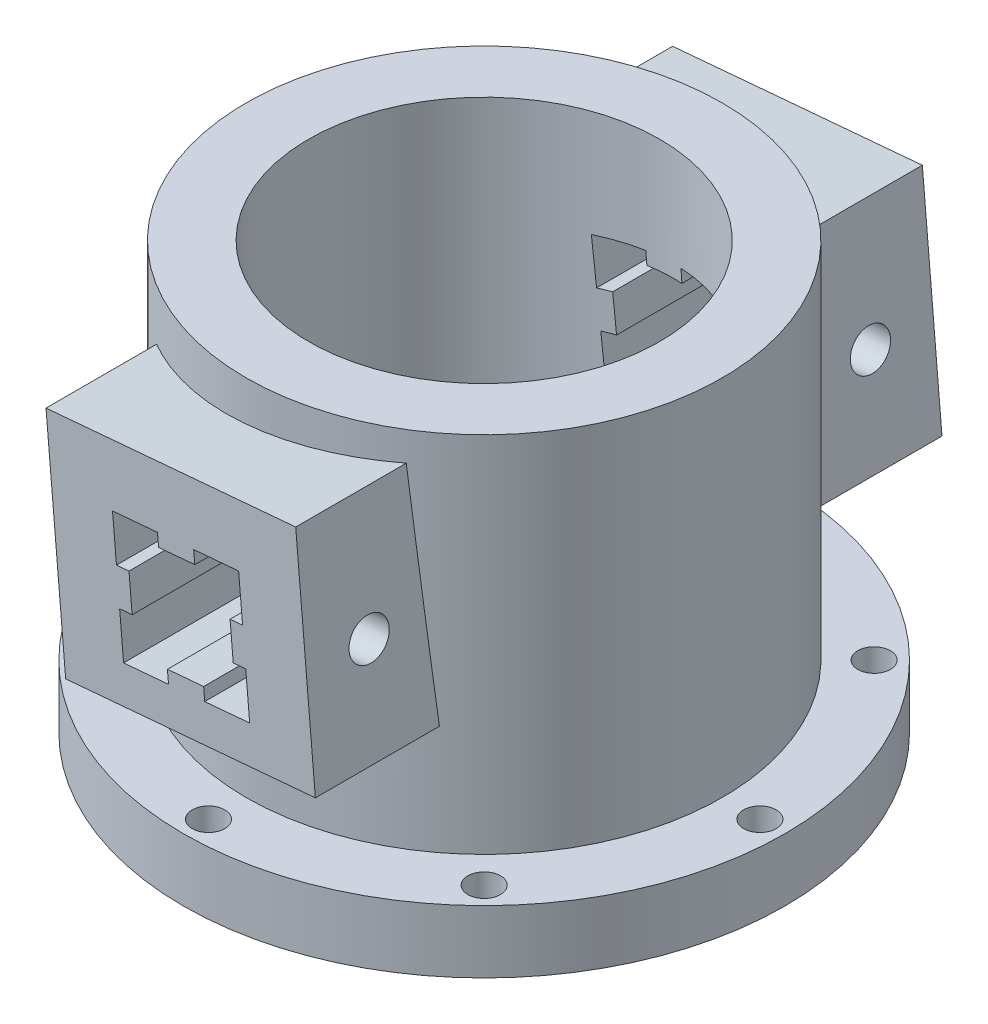
SolidWorks part; units mm, degrees
ref_plane "Front Plane" through (0, 0, 0) normal (0, 0, 1) x (1, 0, 0)
ref_plane "Top Plane" through (0, 0, 0) normal (0, 1, 0) x (1, 0, 0)
ref_plane "Right Plane" through (0, 0, 0) normal (1, 0, 0) x (0, 0, -1)
ref_axis "Axe1" through (0, -1.825, 0) along (0, 1, 0)
sketch "Esquisse1" plane through (0, 0, 0) normal (0, 0, 1) x (1, 0, 0)
  line L0 (14, 0) -> (14, 34)
  line L1 (14, 34) -> (19, 34)
  line L4 (19, 34) -> (19, 5)
  line L5 (19, 5) -> (24, 5)
  line L6 (24, 5) -> (24, 0)
  line L7 (24, 0) -> (14, 0)
  line L8 (0, -1.825) -> (0, 38.325) construction
  dimension "D1" = 14
  dimension "D4" = 5
  dimension "D5" = 24
  dimension "D6" = 5
  dimension "D7" = 34
revolve "Révolution1" add sketch "Esquisse1" angle 360 about axis through (0, -1.825, 0) along (0, 1, 0)
sketch "Esquisse4" plane through (0, 0, 0) normal (0, -1, 0) x (-1, 0, 0)
  circle A0 centre (0, -22) radius 1.3
  dimension "D1" = 2.6
  dimension "D2" = 22
extrude "FixingHole" cut sketch "Esquisse4" against normal through all
pattern_circular "FixingHoleRepetition" count 8 over 360 about axis through (0, 0, 0) along (0, 1, 0) of "FixingHole"
ref_plane "Plan1" through (0, 0, 15) normal (0, 0, 1) x (1, 0, 0)
sketch "Esquisse5" plane through (0, 0, 15) normal (0, 0, 1) x (1, 0, 0)
  line L0 (9.9619, 31.6746) -> (11.5308, 13.7431)
  line L1 (11.5308, 13.7431) -> (-8.3931, 12)
  line L2 (-8.3931, 12) -> (-9.9619, 29.9315)
  line L3 (-9.9619, 29.9315) -> (9.9619, 31.6746)
  line L4 (0, -1.825) -> (0, 38.325) construction
  line L5 (5.408, 26.3575) -> (5.7218, 22.7712)
  line L6 (24, 5) -> (-24, 5) construction
  line L27 (5.7218, 22.7712) -> (4.7241, 22.6839)
  line L28 (4.7241, 22.6839) -> (4.9768, 19.7949)
  line L29 (4.9768, 19.7949) -> (5.9745, 19.8822)
  line L30 (5.9745, 19.8822) -> (6.2883, 16.2959)
  line L31 (6.2883, 16.2959) -> (2.702, 15.9822)
  line L32 (2.702, 15.9822) -> (2.6147, 16.9799)
  line L33 (2.6147, 16.9799) -> (-0.2742, 16.7271)
  line L34 (-0.2742, 16.7271) -> (-0.187, 15.7294)
  line L35 (-0.187, 15.7294) -> (-3.7733, 15.4156)
  line L36 (-3.7733, 15.4156) -> (-4.087, 19.0019)
  line L37 (-4.087, 19.0019) -> (-3.0893, 19.0892)
  line L38 (-3.0893, 19.0892) -> (-3.3421, 21.9782)
  line L39 (-3.3421, 21.9782) -> (-4.3398, 21.8909)
  line L40 (-4.3398, 21.8909) -> (-4.6535, 25.4772)
  line L41 (-4.6535, 25.4772) -> (-1.0672, 25.791)
  line L42 (-1.0672, 25.791) -> (-0.9799, 24.7933)
  line L43 (-0.9799, 24.7933) -> (1.909, 25.046)
  line L44 (1.909, 25.046) -> (1.8217, 26.0437)
  line L45 (1.8217, 26.0437) -> (5.408, 26.3575)
  point P6 (0, 30.8031)
  dimension "D1" = 5
  dimension "D2" = 18
  dimension "D3" = 7
  dimension "D4" = 20
  dimension "D5" = 10.1
  dimension "D6" = 5
  dimension "D7" = 1.0015
  dimension "D10" = 10.1
  dimension "D11" = 3.6
  dimension "D13" = 3
extrude "RightFixing" add sketch "Esquisse5" along normal blind 10
sketch "Esquisse7" plane through (12.6364, 1.1055, 0) normal (0.9962, 0.0872, 0) x (0, 0, -1)
  line L1 (-25, 12.6858) -> (-25, 30.6858) construction
  line L2 (-25, 12.6858) -> (-15.1011, 12.6858) construction
  circle A1 centre (-20, 20.8358) radius 1.6
  dimension "D1" = 3.2
  dimension "D4" = 8.15
  dimension "D5" = 5
extrude "TopFixingHoles" cut sketch "Esquisse7" against normal up to next
mirror "FixingSymetry" about plane through (0, 0, 0) normal (0, 0, 1) of "TopFixingHoles", "RightFixing"
sketch "Esquisse6" plane through (0, 0, 25) normal (0, 0, 1) x (1, 0, 0)
  line L22 (5.408, 26.3575) -> (5.7218, 22.7712)
  line L23 (5.7218, 22.7712) -> (4.7241, 22.6839)
  line L24 (4.7241, 22.6839) -> (4.9768, 19.7949)
  line L25 (4.9768, 19.7949) -> (5.9745, 19.8822)
  line L26 (5.9745, 19.8822) -> (6.2883, 16.2959)
  line L27 (6.2883, 16.2959) -> (2.702, 15.9822)
  line L28 (2.702, 15.9822) -> (2.6147, 16.9799)
  line L29 (2.6147, 16.9799) -> (-0.2742, 16.7271)
  line L30 (-0.2742, 16.7271) -> (-0.187, 15.7294)
  line L31 (-0.187, 15.7294) -> (-3.7733, 15.4156)
  line L32 (-3.7733, 15.4156) -> (-4.087, 19.0019)
  line L33 (-4.087, 19.0019) -> (-3.0893, 19.0892)
  line L34 (-3.0893, 19.0892) -> (-3.3421, 21.9782)
  line L35 (-3.3421, 21.9782) -> (-4.3398, 21.8909)
  line L36 (-4.3398, 21.8909) -> (-4.6535, 25.4772)
  line L37 (-4.6535, 25.4772) -> (-1.0672, 25.791)
  line L38 (-1.0672, 25.791) -> (-0.9799, 24.7933)
  line L39 (-0.9799, 24.7933) -> (1.909, 25.046)
  line L40 (1.909, 25.046) -> (1.8217, 26.0437)
  line L41 (1.8217, 26.0437) -> (5.408, 26.3575)
extrude "HoleForFixing" cut sketch "Esquisse6" against normal through all
